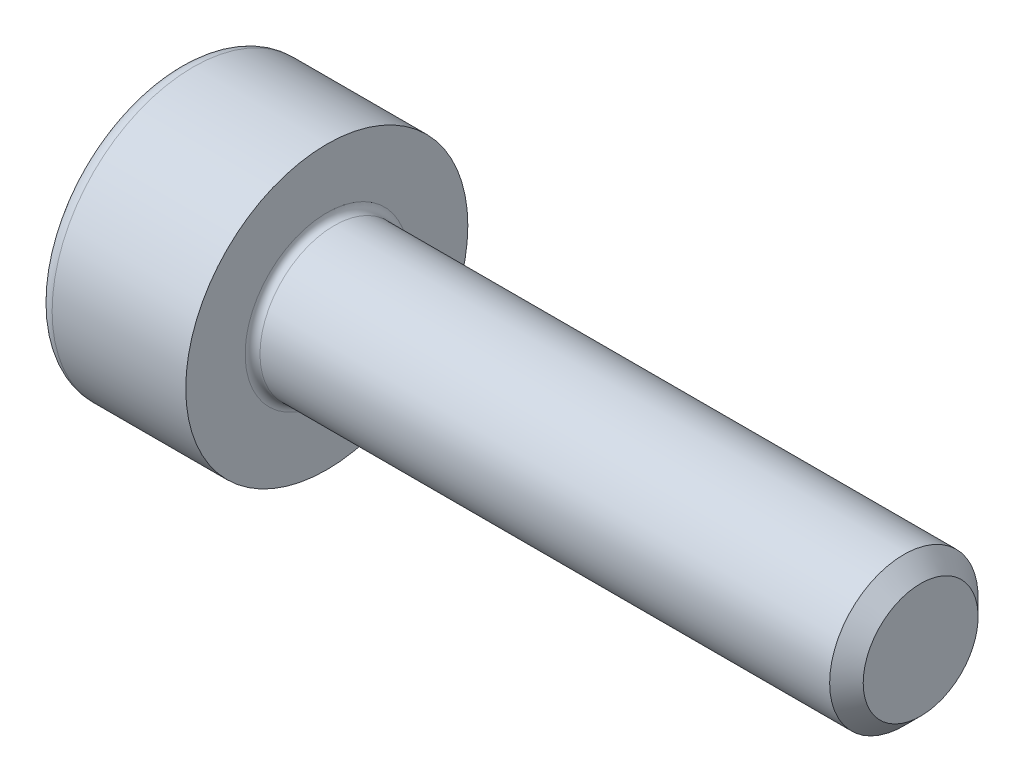
SolidWorks part; units mm, degrees
revolve "Base-Revolve" add sketch "BodySke"
sketch "BodySke" plane through (0, 0, 0) normal (0, 0, 1) x (1, 0, 0)
  line L0 (0, 0) -> (0, 1.9)
  line L1 (0, 1.9) -> (2, 1.9)
  line L2 (2, 1.9) -> (2, 1)
  line L3 (2, 1) -> (9.774, 1)
  line L4 (10, 0.774) -> (10, 0)
  line L5 (10, 0) -> (0, 0)
  line L6 (-31.75, 0) -> (127, 0) construction
  line L8 (10, 0.774) -> (9.774, 1)
  line L10 (10, -0.774) -> (9.774, -1) construction
  line L11 (2.4, 9.525) -> (2.4, 3.175) construction
  line L12 (2, 9.525) -> (2, 3.175) construction
  line L13 (-50, 9.525) -> (-50, 3.175) construction
  dimension "Head_ht" = 2
  dimension "Length" = 8
  dimension "Body_ch_ang" = 45
  dimension "Diameter" = 2
  dimension "Minor_dia" = 1.548
  dimension "Advance" = 0.4
  dimension "Thread_nom" = 8
  dimension "Thread_length" = 60
  dimension "Head_dia" = 3.8
cosmetic thread "ThreadCosmetic"
fillet "Fillet1" radius 0.1 1 edges at (2, 0, 1)
fillet "Fillet2" radius 0.2 1 edges at (0, 0, 1.9)
ref_plane "Plane1" through (0, 0, 0) normal (0, 0, 1) x (1, 0, 0)
ref_plane "Plane2" through (0, 0, 0) normal (0, 1, 0) x (1, 0, 0)
ref_plane "Plane3" through (0, 0, 0) normal (1, 0, 0) x (0, 0, -1)
sketch "Sketch2" plane through (0, 0, 0) normal (0, 0, 1) x (1, 0, 0)
  line L0 (0, 0.76) -> (1, 0.76)
  line L1 (1, 0.76) -> (1.4388, 0)
  line L2 (-31.75, 0) -> (127, 0) construction
  line L3 (1.4388, 0) -> (0, 0)
  line L4 (0, 0) -> (0, 0.76)
  line L6 (0, 0) -> (47.625, 0) construction
  dimension "D1" = 0.76
  dimension "D2" = 60
  dimension "Depth" = 1
revolve "Hex-PreBroach" cut sketch "Sketch2" angle 360 about L6
sketch "Sketch3" plane through (0, 0, 0) normal (-1, 0, 0) x (0, 0.5, 0.866)
  line L0 (0.4388, 0.76) -> (-0.4388, 0.76)
  line L1 (-0.4388, 0.76) -> (-0.8776, 0)
  line L2 (0.4388, 0.76) -> (0.8776, 0)
  line L3 (0.4388, -0.76) -> (0.8776, 0)
  line L4 (0.4388, -0.76) -> (-0.4388, -0.76)
  line L5 (-0.4388, -0.76) -> (-0.8776, 0)
  dimension "D1" = 0.76
  dimension "D2" = 0.76
  dimension "Hex_size" = 1.52
extrude "Hex" cut sketch "Sketch3" against normal blind 1
sketch "ThdSchSke" plane through (0, 0, 0) normal (0, 0, 1) x (1, 0, 0)
  line L0 (3.2, -0.774) -> (3.0418, -1)
  line L1 (3.2, -0.774) -> (3.3582, -1)
  line L2 (3.3582, -1) -> (3.3582, -1.25)
  line L3 (-3.175, 0) -> (5.1513, 0) construction
  line L4 (0, 1.7) -> (0, -1.7) construction
  line L5 (3.3582, -1.25) -> (3.0418, -1.25)
  line L6 (3.0418, -1.25) -> (3.0418, -1)
  dimension "Thread_minor" = 1.548
  dimension "Diameter" = 2
  dimension "Start" = 3.2
revolve "ThreadSchematic" [suppressed] cut sketch "ThdSchSke" angle 360 about L3
pattern_linear "ThdSchPat" [suppressed]
equation "\"D2@Sketch3\" = \"Hex_size@Sketch3\" / 2"
equation "\"D1@Sketch3\" = \"Hex_size@Sketch3\" / 2"
equation "\"D1@Sketch2\" = \"Hex_size@Sketch3\" / 2"
equation "\"Thread_minor@ThreadCosmetic\"  =  \"Minor_dia@BodySke\""
equation "\"Depth@Sketch2\" =  \"Key_eng@Hex\""
equation "\"Thread_length@ThreadCosmetic\" = ((sgn( (\"Length@BodySke\" - \"Advance@BodySke\" * 3.0) - \"Thread_nom@BodySke\" )-1)*( (\"Length@BodySke\" - \"Advance@BodySke\" * 3.0) - \"Thread_nom@BodySke\" ))/-2+ \"Thread_nom@BodySke\""
equation "\"Thread_minor@ThdSchSke\" = \"Minor_dia@BodySke\""
equation "\"Diameter@ThdSchSke\" = \"Diameter@BodySke\""
equation "\"Overcut@ThdSchSke\" = \"Diameter@BodySke\" * 1.25"
equation "\"Start@ThdSchSke\" = \"Head_ht@BodySke\" + \"Length@BodySke\" - \"Thread_length@ThreadCosmetic\"  '---Non-countersunk---"
equation "\"Num_threads@ThdSchPat\" = int( \"Thread_length@ThreadCosmetic\" / \"Advance@BodySke\" + 0.999 )  + 1"
equation "\"Advance@ThdSchPat\" = \"Thread_length@ThreadCosmetic\" /  (\"Num_threads@ThdSchPat\" - 1) 'relax it"
equation "\"Num_threads@ThdSchPat\" = \"Num_threads@ThdSchPat\" - sgn( \"Num_threads@ThdSchPat\" - 1) '---chamfered tips only---"
